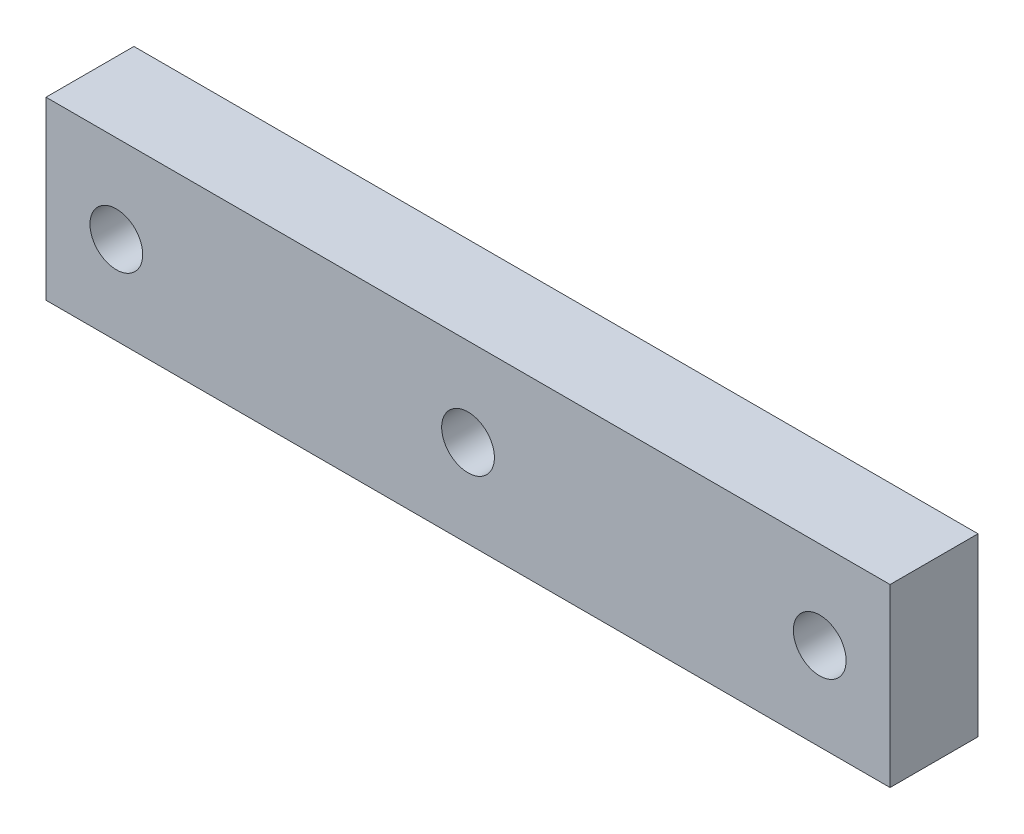
SolidWorks part; units mm, degrees
ref_plane "Alzado" through (0, 0, 0) normal (0, 0, 1) x (1, 0, 0)
ref_plane "Planta" through (0, 0, 0) normal (0, 1, 0) x (1, 0, 0)
ref_plane "Vista lateral" through (0, 0, 0) normal (1, 0, 0) x (0, 0, -1)
sketch "Croquis1" plane through (0, 0, 0) normal (0, 0, 1) x (1, 0, 0)
  line L1 (0, 0) -> (336, 0)
  line L2 (0, 0) -> (0, 70)
  line L3 (0, 70) -> (336, 70)
  line L4 (336, 0) -> (336, 70)
  circle A0 centre (308, 35) radius 10.5
  circle A1 centre (168, 35) radius 10.5
  circle A2 centre (28, 35) radius 10.5
  point P11 (336, 35)
  dimension "D3" = 28
  dimension "D4" = 28
  dimension "D6" = 140
  dimension "D7" = 35
  dimension "D8" = 21
  dimension "D9" = 21
  dimension "D10" = 35
  dimension "D1" = 336
  dimension "D2" = 70
extrude "Saliente-Extruir1" add sketch "Croquis1" along normal blind 35
